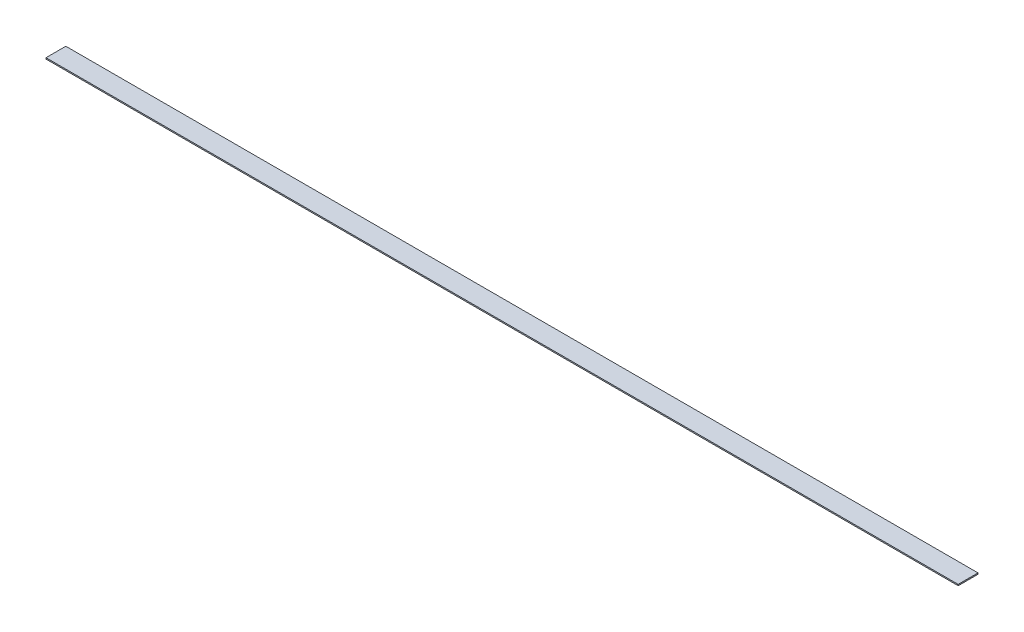
SolidWorks part; units mm, degrees
material "Very Low Density PE (SS)"
ref_plane "Front Plane" through (0, 0, 0) normal (0, 0, 1) x (1, 0, 0)
ref_plane "Top Plane" through (0, 0, 0) normal (0, 1, 0) x (1, 0, 0)
ref_plane "Right Plane" through (0, 0, 0) normal (1, 0, 0) x (0, 0, -1)
sketch "Sketch1" plane through (0, 0, 0) normal (0, 1, 0) x (1, 0, 0)
  line L1 (584.2, -12.7) -> (-584.2, -12.7)
  line L2 (584.2, -12.7) -> (584.2, 12.7)
  line L3 (584.2, 12.7) -> (-584.2, 12.7)
  line L4 (-584.2, -12.7) -> (-584.2, 12.7)
  line L5 (584.2, -12.7) -> (-584.2, 12.7) construction
  line L6 (584.2, 12.7) -> (-584.2, -12.7) construction
  point P0 (0, 0)
  dimension "D1" = 1168.4
  dimension "D2" = 25.4
extrude "Boss-Extrude1" add sketch "Sketch1" along normal blind 1.5875
